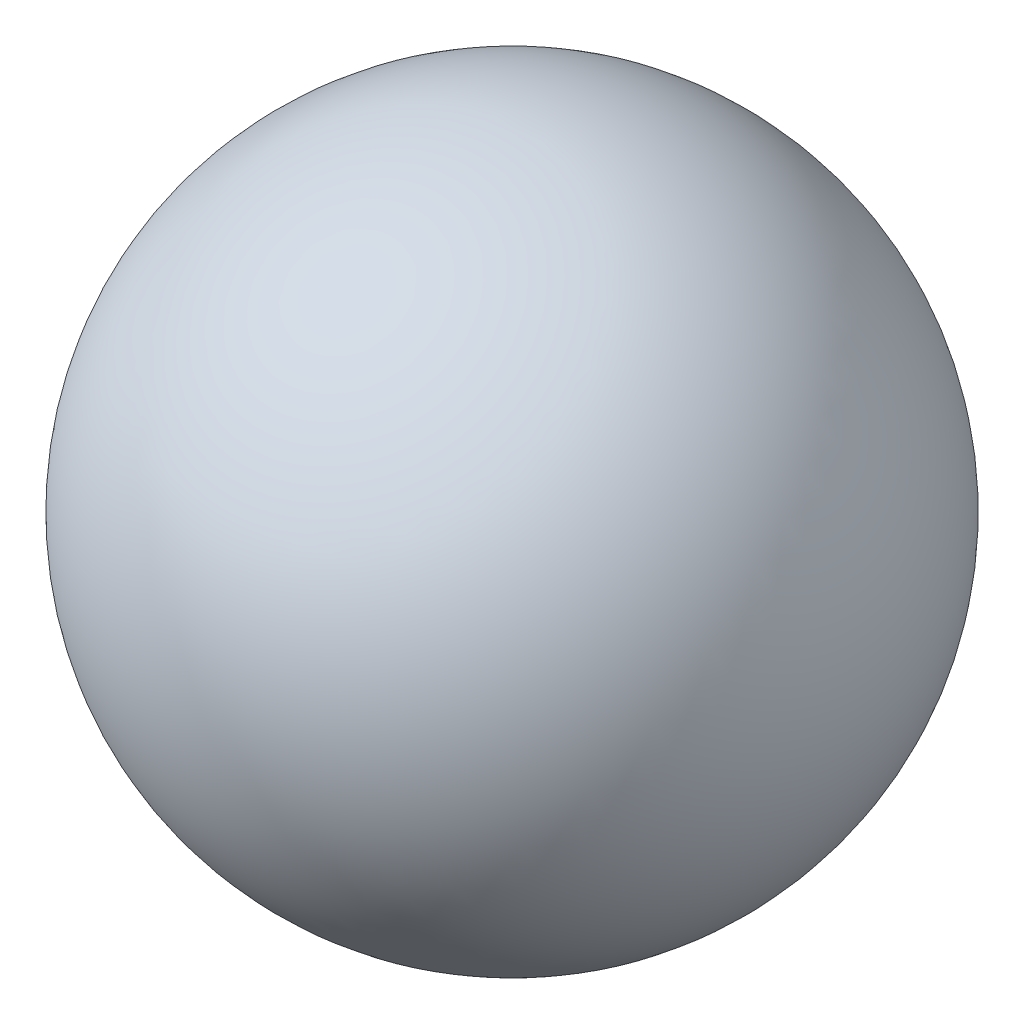
SolidWorks part; units mm, degrees
ref_plane "Alzado" through (0, 0, 0) normal (0, 0, 1) x (1, 0, 0)
ref_plane "Planta" through (0, 0, 0) normal (0, 1, 0) x (1, 0, 0)
ref_plane "Vista lateral" through (0, 0, 0) normal (1, 0, 0) x (0, 0, -1)
sketch "Croquis1" plane through (0, 0, 0) normal (0, 0, 1) x (1, 0, 0)
  line L0 (0, 7.5) -> (0, -7.5)
  arc A0 (0, 7.5) -> (0, -7.5) centre (0, 0) ccw
  dimension "D1" = 15
revolve "Revolución3" add sketch "Croquis1" angle 360 about L0
